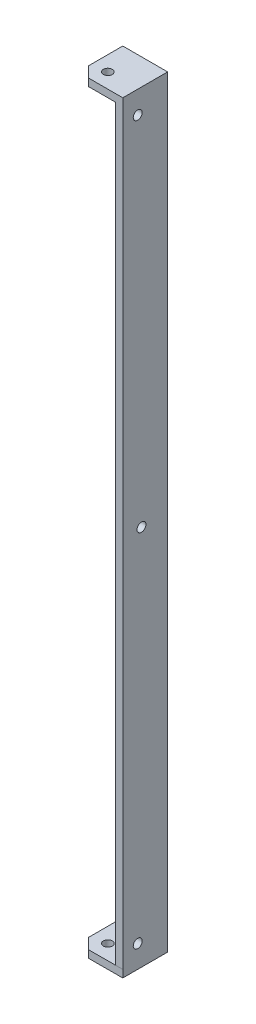
SolidWorks part; units mm, degrees
material "ABS"
ref_plane "Front Plane" through (0, 0, 0) normal (0, 0, 1) x (1, 0, 0)
ref_plane "Top Plane" through (0, 0, 0) normal (0, 1, 0) x (1, 0, 0)
ref_plane "Right Plane" through (0, 0, 0) normal (1, 0, 0) x (0, 0, -1)
sketch "Sketch1" plane through (0, 0, 0) normal (0, 0, 1) x (1, 0, 0)
  line L0 (-2.5, -240) -> (-2.5, 240) construction
  line L1 (-12.5, -250) -> (12.5, -250)
  line L2 (-12.5, -250) -> (-12.5, 250)
  line L3 (-12.5, 250) -> (12.5, 250)
  line L4 (12.5, -250) -> (12.5, 250)
  line L5 (-12.5, -250) -> (12.5, 250) construction
  line L6 (-12.5, 250) -> (12.5, -250) construction
  circle A0 centre (-2.5, 240) radius 3
  circle A1 centre (-2.5, -240) radius 3
  circle A2 centre (0, 0) radius 3
  point P0 (0, 0)
  dimension "D3" = 6
  dimension "D5" = 6
  dimension "D7" = 6
  dimension "D1" = 25
  dimension "D2" = 500
  dimension "D4" = 10
  dimension "D6" = 10
  dimension "D8" = 10
extrude "Boss-Extrude1" add sketch "Sketch1" along normal blind 5
sketch "Sketch2" plane through (0, 0, 0) normal (0, 0, -1) x (-1, 0, 0)
  line L0 (-12.5, -250) -> (-12.5, 250) construction
  line L1 (-12.5, 250) -> (-17.5, 250)
  line L2 (-12.5, 250) -> (-12.5, -250)
  line L3 (-12.5, -250) -> (-17.5, -250)
  line L4 (-17.5, 250) -> (-17.5, -250)
  line L5 (-12.5, 250) -> (12.5, 250) construction
  point P8 (-12.5, -250)
  dimension "D1" = 5
extrude "Boss-Extrude2" add sketch "Sketch2" against normal blind 30
sketch "Sketch3" plane through (12.5, 0, 0) normal (-1, 0, 0) x (0, 0, 1)
  line L0 (20, 240) -> (20, -240) construction
  line L1 (30, -250) -> (5, -250) construction
  line L2 (30, 250) -> (5, 250) construction
  line L4 (30, -250) -> (30, 250) construction
  circle A0 centre (20, -240) radius 3
  circle A1 centre (17.5, 0) radius 3
  circle A2 centre (20, 240) radius 3
  dimension "D1" = 6
  dimension "D2" = 10
  dimension "D3" = 10
  dimension "D4" = 10
extrude "Cut-Extrude1" cut sketch "Sketch3" against normal blind 20.5
sketch "Sketch4" plane through (0, 250, 0) normal (0, 1, 0) x (1, 0, 0)
  line L4 (-12.5, 0) -> (17.5, 0)
  line L6 (-12.5, -22.9289) -> (-12.5, 0)
  line L7 (-12.5, -22.9289) -> (-5.4289, -30)
  line L8 (-5.4289, -30) -> (17.5, -30)
  line L9 (17.5, -30) -> (17.5, 0)
  circle A0 centre (-2.5, -20) radius 3
  dimension "D1" = 6
  dimension "D2" = 20
  dimension "D3" = 20
  dimension "D4" = 10
extrude "Boss-Extrude3" add sketch "Sketch4" along normal blind 5
sketch "Sketch5" plane through (0, -250, 0) normal (0, -1, 0) x (-1, 0, 0)
  line L5 (12.5, 0) -> (-17.5, 0)
  line L7 (-17.5, 0) -> (-17.5, -30)
  line L8 (-17.5, -30) -> (5.4563, -30.0547)
  line L9 (5.4563, -30.0547) -> (12.5, -22.9564)
  line L10 (12.5, -22.9564) -> (12.5, 0)
  circle A0 centre (2.5, -20) radius 3
  dimension "D1" = 6
  dimension "D2" = 20
  dimension "D3" = 20
  dimension "D4" = 10
extrude "Boss-Extrude4" add sketch "Sketch5" along normal blind 5
